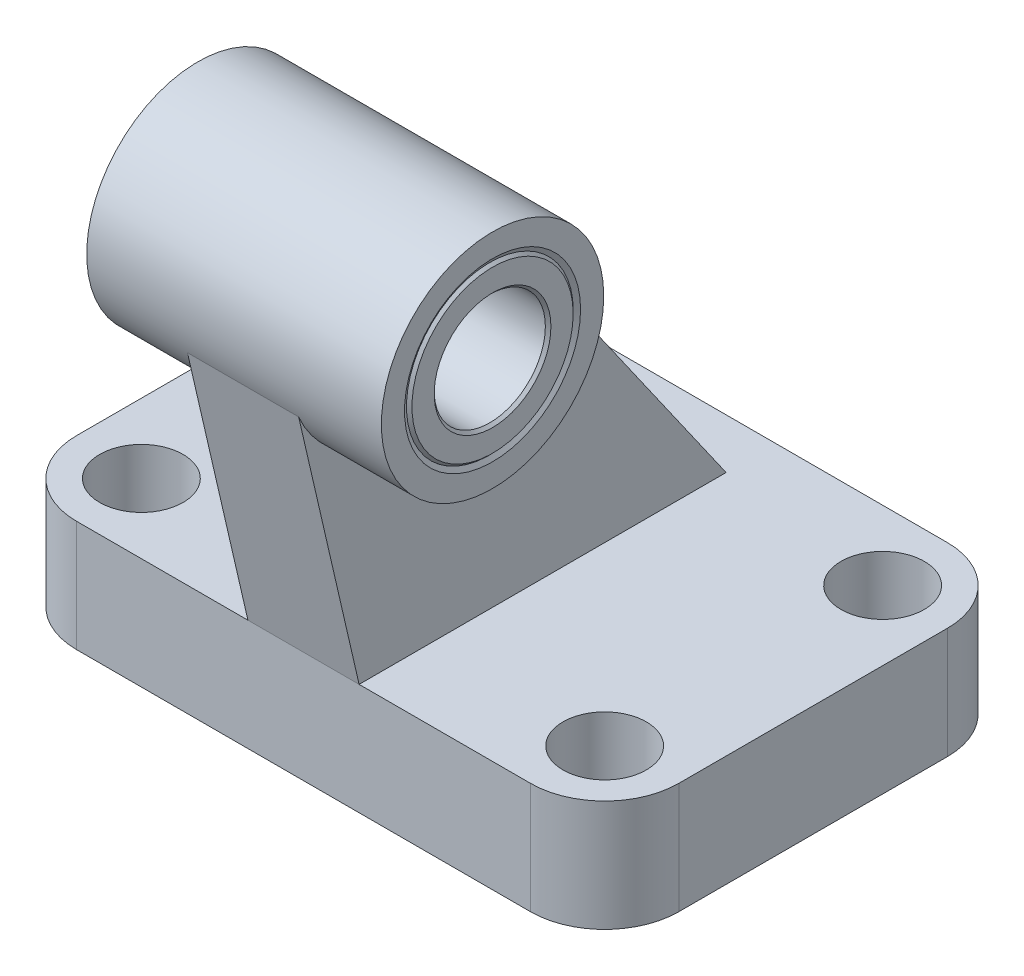
SolidWorks part; units mm, degrees
ref_plane "Front Plane" through (0, 0, 0) normal (0, 0, 1) x (1, 0, 0)
ref_plane "Top Plane" through (0, 0, 0) normal (0, 1, 0) x (1, 0, 0)
ref_plane "Right Plane" through (0, 0, 0) normal (1, 0, 0) x (0, 0, -1)
ref_plane "Plane1" through (0, 0, 0) normal (0, 1, 0) x (1, 0, 0)
sketch "Sketch1" plane through (0, 0, 0) normal (0, 1, 0) x (1, 0, 0)
  line L0 (-24.5, -22.5) -> (24.5, -22.5)
  line L1 (32.5, -14.5) -> (32.5, 14.5)
  line L2 (24.5, 22.5) -> (-24.5, 22.5)
  line L3 (-32.5, 14.5) -> (-32.5, -14.5)
  arc A0 (-32.5, -14.5) -> (-24.5, -22.5) centre (-24.5, -14.5) ccw
  arc A1 (24.5, -22.5) -> (32.5, -14.5) centre (24.5, -14.5) ccw
  arc A2 (32.5, 14.5) -> (24.5, 22.5) centre (24.5, 14.5) ccw
  arc A3 (-24.5, 22.5) -> (-32.5, 14.5) centre (-24.5, 14.5) ccw
extrude "Boss-Extrude1" add sketch "Sketch1" along normal blind 12
ref_plane "Plane2" through (0, 0, 0) normal (1, 0, 0) x (0, 0, -1)
sketch "Sketch2" plane through (0, 0, 0) normal (1, 0, 0) x (0, 0, -1)
  line L0 (-29.5054, 42.3438) -> (-22.5, 12)
  line L1 (-22.5, 12) -> (17.1068, 12)
  line L2 (17.1068, 12) -> (-7.6699, 47.3849)
  line L3 (-7.6699, 47.3849) -> (-29.5054, 42.3438)
extrude "Boss-Extrude2" add sketch "Sketch2" against normal blind 6 and the other way blind 6
ref_plane "Plane3" through (0, 0, 0) normal (1, 0, 0) x (0, 0, -1)
sketch "Sketch3" plane through (0, 0, 0) normal (1, 0, 0) x (0, 0, -1)
  circle A0 centre (-18, 45) radius 12
extrude "Boss-Extrude3" add sketch "Sketch3" against normal blind 15.9 and the other way blind 15.9
ref_plane "Plane4" through (0, 0, 15) normal (0, 0, 1) x (1, 0, 0)
sketch "Sketch4" plane through (0, 0, 15) normal (0, 0, 1) x (1, 0, 0)
  line L0 (-25, 0) -> (-29.5, 0)
  line L1 (-29.5, 0) -> (-29.5, 12)
  line L2 (-29.5, 12) -> (-25, 12)
  line L3 (-25, 12) -> (-25, 0)
  line L4 (-25, 12) -> (-25, 0) construction
revolve "Cut-Revolve1" cut sketch "Sketch4" angle 360 about L4
ref_plane "Plane5" through (0, 0, 15) normal (0, 0, 1) x (1, 0, 0)
sketch "Sketch5" plane through (0, 0, 15) normal (0, 0, 1) x (1, 0, 0)
  line L0 (25, 0) -> (20.5, 0)
  line L1 (20.5, 0) -> (20.5, 12)
  line L2 (20.5, 12) -> (25, 12)
  line L3 (25, 12) -> (25, 0)
  line L4 (25, 12) -> (25, 0) construction
revolve "Cut-Revolve2" cut sketch "Sketch5" angle 360 about L4
ref_plane "Plane6" through (0, 0, -15) normal (0, 0, 1) x (1, 0, 0)
sketch "Sketch6" plane through (0, 0, -15) normal (0, 0, 1) x (1, 0, 0)
  line L0 (-25, 0) -> (-29.5, 0)
  line L1 (-29.5, 0) -> (-29.5, 12)
  line L2 (-29.5, 12) -> (-25, 12)
  line L3 (-25, 12) -> (-25, 0)
  line L4 (-25, 12) -> (-25, 0) construction
revolve "Cut-Revolve3" cut sketch "Sketch6" angle 360 about L4
ref_plane "Plane7" through (0, 0, -15) normal (0, 0, 1) x (1, 0, 0)
sketch "Sketch7" plane through (0, 0, -15) normal (0, 0, 1) x (1, 0, 0)
  line L0 (25, 0) -> (20.5, 0)
  line L1 (20.5, 0) -> (20.5, 12)
  line L2 (20.5, 12) -> (25, 12)
  line L3 (25, 12) -> (25, 0)
  line L4 (25, 12) -> (25, 0) construction
revolve "Cut-Revolve4" cut sketch "Sketch7" angle 360 about L4
ref_plane "Plane8" through (0, 0, 18) normal (0, 0, 1) x (1, 0, 0)
sketch "Sketch8" plane through (0, 0, 18) normal (0, 0, 1) x (1, 0, 0)
  line L0 (-15.9, 45) -> (-15.9, 54.5)
  line L1 (-15.9, 54.5) -> (-15.6113, 54)
  line L2 (-15.6113, 54) -> (15.6113, 54)
  line L3 (15.6113, 54) -> (15.9, 54.5)
  line L4 (15.9, 54.5) -> (15.9, 45)
  line L5 (15.9, 45) -> (-15.9, 45)
  line L6 (15.9, 45) -> (-15.9, 45) construction
revolve "Cut-Revolve5" cut sketch "Sketch8" angle 360 about L6
ref_plane "Plane9" through (0, 0, 18) normal (0, 0, 1) x (1, 0, 0)
sketch "Sketch9" plane through (0, 0, 18) normal (0, 0, 1) x (1, 0, 0)
  line L0 (-15.9, 51.3) -> (-15.6, 51)
  line L1 (-15.6, 51) -> (15.6, 51)
  line L2 (15.6, 51) -> (15.9, 51.3)
  line L3 (15.9, 51.3) -> (15.9, 53.7)
  line L4 (15.9, 53.7) -> (15.6, 54)
  line L5 (15.6, 54) -> (-15.6, 54)
  line L6 (-15.6, 54) -> (-15.9, 53.7)
  line L7 (-15.9, 53.7) -> (-15.9, 51.3)
  line L8 (15.9, 45) -> (-15.9, 45) construction
revolve "Revolve1" add sketch "Sketch9" angle 360 about L8
